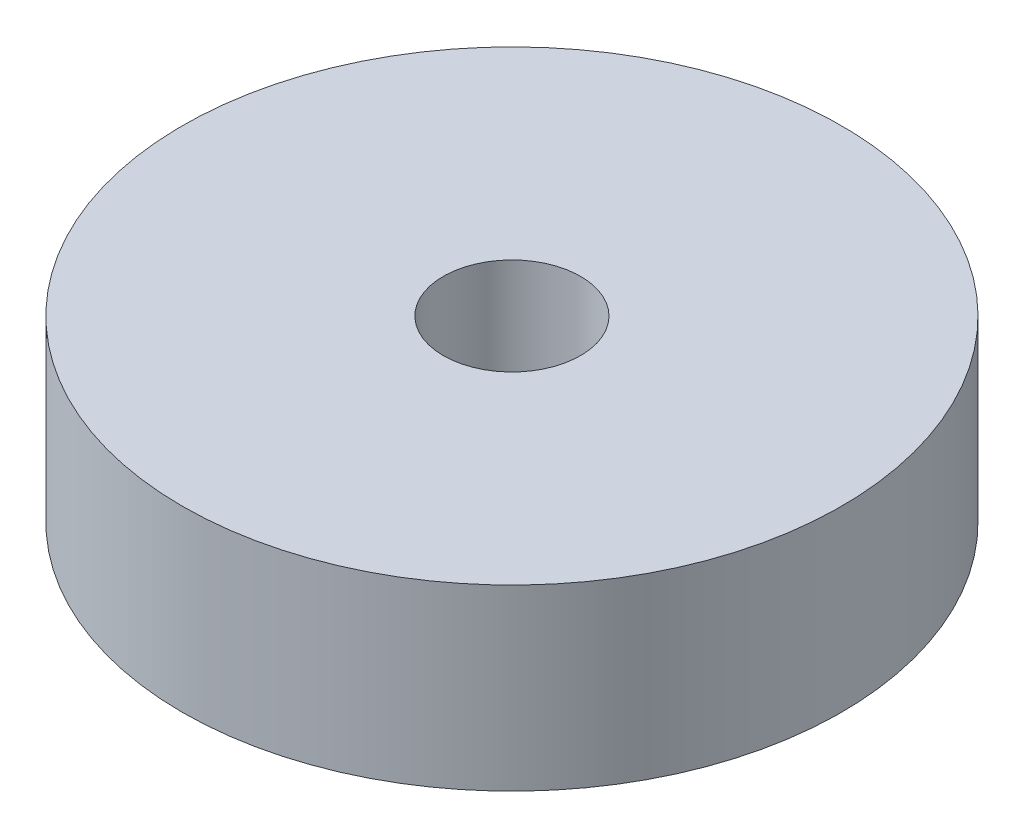
SolidWorks part; units mm, degrees
ref_plane "Front Plane" through (0, 0, 0) normal (0, 0, 1) x (1, 0, 0)
ref_plane "Top Plane" through (0, 0, 0) normal (0, 1, 0) x (1, 0, 0)
ref_plane "Right Plane" through (0, 0, 0) normal (1, 0, 0) x (0, 0, -1)
sketch "Sketch1" plane through (0, 0, 0) normal (0, 1, 0) x (1, 0, 0)
  circle A0 centre (0, 0) radius 24
  dimension "D1" = 48
extrude "Boss-Extrude1" add sketch "Sketch1" along normal blind 13
sketch "Sketch2" plane through (0, 13, 0) normal (0, 1, 0) x (1, 0, 0)
  circle A0 centre (0, 0) radius 5
  dimension "D1" = 10
extrude "Cut-Extrude1" cut sketch "Sketch2" against normal blind 10
sketch "Sketch3" plane through (0, 0, 0) normal (0, -1, 0) x (-1, 0, 0)
  line L1 (11, -11) -> (-11, -11)
  line L2 (11, -11) -> (11, 11)
  line L3 (11, 11) -> (-11, 11)
  line L4 (-11, -11) -> (-11, 11)
  circle A0 centre (11, -11) radius 1.5
  circle A1 centre (-11, -11) radius 1.5
  circle A2 centre (11, 11) radius 1.5
  circle A3 centre (-11, 11) radius 1.5
  point P8 (0, -11)
  point P10 (-11, 0)
  dimension "D1" = 3
  dimension "D2" = 22
extrude "Cut-Extrude2" cut sketch "Sketch3" against normal blind 8 contours L1 A0 L2 | L2 A0 L1 | L4 A1 L1 | L1 A1 L4 | A2 | A3
